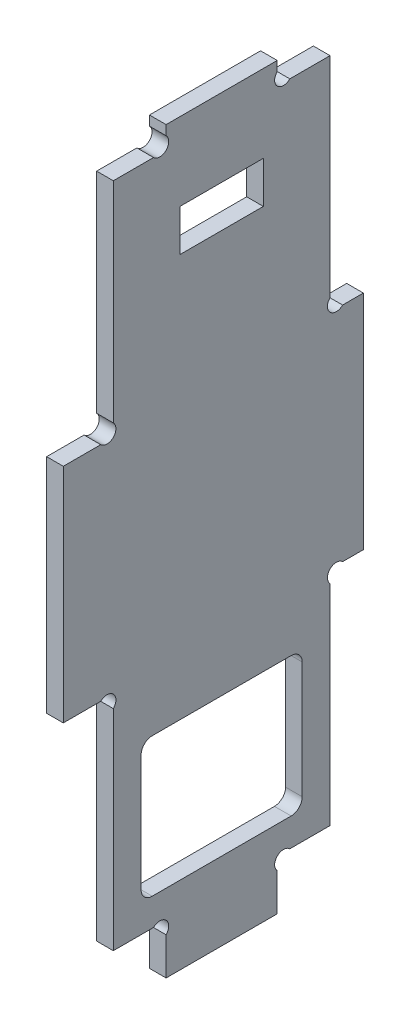
SolidWorks part; units mm, degrees
ref_plane "Plan de face" through (0, 0, 0) normal (0, 0, 1) x (1, 0, 0)
ref_plane "Plan de dessus" through (0, 0, 0) normal (0, 1, 0) x (1, 0, 0)
ref_plane "Plan de droite" through (0, 0, 0) normal (1, 0, 0) x (0, 0, -1)
sketch "Esquisse1" plane through (0, 0, 0) normal (1, 0, 0) x (0, 0, -1)
  line L13 (18.5, 6.7373) -> (18.5, 0)
  line L15 (16.2373, 9) -> (9, 9)
  line L17 (50.2627, 49) -> (54, 49)
  line L18 (6.7373, 49) -> (0, 49)
  line L19 (38.5, 6.7373) -> (38.5, 0)
  line L20 (50.2627, 89) -> (54, 89)
  line L21 (6.7373, 89) -> (0, 89)
  line L22 (18.5, 0) -> (38.5, 0)
  line L23 (40.7627, 9) -> (48, 9)
  line L24 (48, 9) -> (48, 46.7373)
  line L25 (9, 9) -> (9, 46.7373)
  line L26 (54, 89) -> (54, 49)
  line L27 (0, 49) -> (0, 89)
  line L29 (18.5, 131.2627) -> (18.5, 133)
  line L30 (38.5, 131.2627) -> (38.5, 133)
  line L31 (9, 91.2627) -> (9, 129)
  line L32 (9, 129) -> (16.2373, 129)
  line L33 (18.5, 133) -> (38.5, 133)
  line L34 (40.7627, 129) -> (48, 129)
  line L35 (48, 129) -> (48, 91.2627)
  arc A0 (50.2627, 49) -> (48, 46.7373) centre (49.1314, 47.8686) ccw
  arc A1 (9, 46.7373) -> (6.7373, 49) centre (7.8686, 47.8686) ccw
  arc A2 (18.5, 6.7373) -> (16.2373, 9) centre (17.3686, 7.8686) ccw
  arc A3 (38.5, 6.7373) -> (40.7627, 9) centre (39.6314, 7.8686) cw
  arc A4 (9, 91.2627) -> (6.7373, 89) centre (7.8686, 90.1314) cw
  arc A5 (50.2627, 89) -> (48, 91.2627) centre (49.1314, 90.1314) cw
  arc A6 (16.2373, 129) -> (18.5, 131.2627) centre (17.3686, 130.1314) ccw
  arc A7 (40.7627, 129) -> (38.5, 131.2627) centre (39.6314, 130.1314) cw
  point P1 (12.6186, 9)
  dimension "D14" = 1.1314
  dimension "D15" = 1.1314
  dimension "D17" = 1.1314
  dimension "D23" = 1.1314
  dimension "D10" = 1.6
  dimension "D1" = 6
  dimension "D2" = 9
  dimension "D3" = 9.5
  dimension "D4" = 9.5
  dimension "D5" = 9
  dimension "D6" = 40
  dimension "D7" = 40
  dimension "D8" = 40
  dimension "D9" = 4
  dimension "D11" = 1.1314
  dimension "D12" = 1.1314
  dimension "D13" = 1.1314
  dimension "D16" = 20
  dimension "D18" = 1.1314
  dimension "D19" = 1.1314
  dimension "D20" = 1.1314
  dimension "D21" = 1.1314
  dimension "D22" = 1.1314
  dimension "D24" = 3.7373
  dimension "D25" = 1.7373
  dimension "D26" = 1.1314
  dimension "D27" = 7.2373
  dimension "D28" = 1.1314
  dimension "D29" = 1.7373
  dimension "D30" = 20
  dimension "D31" = 39
  dimension "D32" = 39
extrude "Extrusion1" add sketch "Esquisse1" along normal blind 3
sketch "Esquisse2" plane through (3, 0, 0) normal (1, 0, 0) x (0, 0, -1)
  line L0 (9, 46.7373) -> (9, 9) construction
  line L1 (14, 14) -> (43, 14)
  line L2 (14, 14) -> (14, 39)
  line L3 (14, 39) -> (43, 39)
  line L4 (43, 14) -> (43, 39)
  line L5 (48, 9) -> (48, 46.7373) construction
  line L6 (9, 9) -> (16.2373, 9) construction
  dimension "D1" = 5
  dimension "D2" = 5
  dimension "D3" = 5
  dimension "D4" = 25
extrude "Enlèv. mat.-Extru.1" cut sketch "Esquisse2" against normal through all
fillet "Congé1" radius 2 4 edges at (1.5, 14, -43) (1.5, 14, -14) (1.5, 39, -14) (1.5, 39, -43)
sketch "Esquisse3" plane through (3, 0, 0) normal (1, 0, 0) x (0, 0, -1)
  line L0 (16.2373, 129) -> (9, 129) construction
  line L1 (21, 119) -> (36, 119)
  line L2 (21, 119) -> (21, 111.5)
  line L3 (21, 111.5) -> (36, 111.5)
  line L4 (36, 119) -> (36, 111.5)
  line L5 (38.5, 133) -> (18.5, 133) construction
  point P6 (28.5, 119)
  point P7 (28.5, 133)
  point P8 (0, 0)
  dimension "D1" = 15
  dimension "D2" = 7.5
  dimension "D3" = 10
extrude "Enlèv. mat.-Extru.2" cut sketch "Esquisse3" against normal through all
